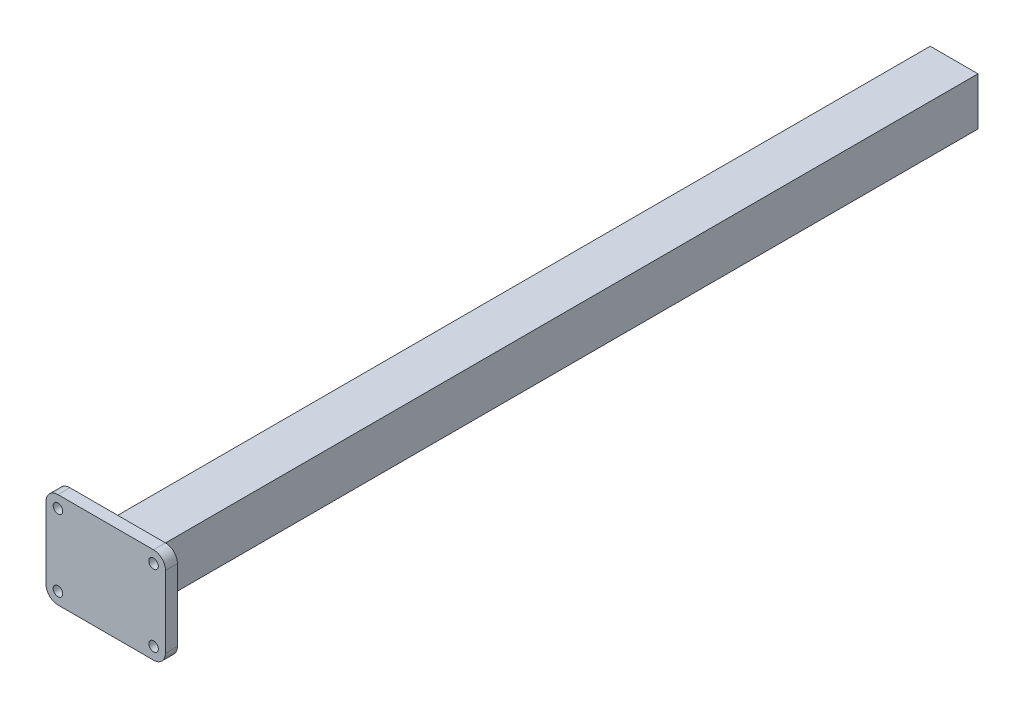
SolidWorks part; units mm, degrees
ref_plane "Plan de face" through (0, 0, 0) normal (0, 0, 1) x (1, 0, 0)
ref_plane "Plan de dessus" through (0, 0, 0) normal (0, 1, 0) x (1, 0, 0)
ref_plane "Plan de droite" through (0, 0, 0) normal (1, 0, 0) x (0, 0, -1)
sketch "Esquisse1" plane through (0, 0, 0) normal (0, 0, 1) x (1, 0, 0)
  line L1 (-20, -20) -> (20, -20)
  line L2 (-20, -20) -> (-20, 20)
  line L3 (-20, 20) -> (20, 20)
  line L4 (20, -20) -> (20, 20)
  line L5 (-20, -20) -> (20, 20) construction
  line L6 (-20, 20) -> (20, -20) construction
  line L7 (-18.5, -18.5) -> (18.5, -18.5)
  line L8 (-18.5, -18.5) -> (-18.5, 18.5)
  line L9 (-18.5, 18.5) -> (18.5, 18.5)
  line L10 (18.5, -18.5) -> (18.5, 18.5)
  line L11 (-18.5, -18.5) -> (18.5, 18.5) construction
  line L12 (-18.5, 18.5) -> (18.5, -18.5) construction
  point P0 (0, 0)
  point P6 (0, 0)
  dimension "D1" = 40
  dimension "D2" = 40
  dimension "D3" = 37
  dimension "D4" = 37
extrude "Boss.-Extru.1" add sketch "Esquisse1" along normal blind 700
sketch "Esquisse2" plane through (0, 0, 700) normal (0, 0, 1) x (1, 0, 0)
  line L1 (-40, -40) -> (40, -40)
  line L2 (-50, -30) -> (-50, 30)
  line L3 (-40, 40) -> (40, 40)
  line L4 (50, -30) -> (50, 30)
  line L5 (-50, -40) -> (50, 40) construction
  line L6 (-50, 40) -> (50, -40) construction
  arc A0 (-40, -40) -> (-50, -30) centre (-40, -30) cw
  arc A1 (40, -40) -> (50, -30) centre (40, -30) ccw
  arc A2 (40, 40) -> (50, 30) centre (40, 30) cw
  arc A3 (-50, 30) -> (-40, 40) centre (-40, 30) cw
  point P0 (0, 0)
  dimension "D3" = 10
  dimension "D1" = 100
  dimension "D2" = 80
extrude "Boss.-Extru.2" add sketch "Esquisse2" along normal blind 10
sketch "Esquisse3" plane through (0, 0, 700) normal (0, 0, -1) x (-1, 0, 0)
  circle A0 centre (40, 30) radius 4
  circle A1 centre (-40, 30) radius 4
  circle A2 centre (-40, -30) radius 4
  circle A3 centre (40, -30) radius 4
  dimension "D1" = 8
  dimension "D2" = 8
  dimension "D3" = 8
  dimension "D4" = 8
extrude "Enlèv. mat.-Extru.1" cut sketch "Esquisse3" against normal blind 10
